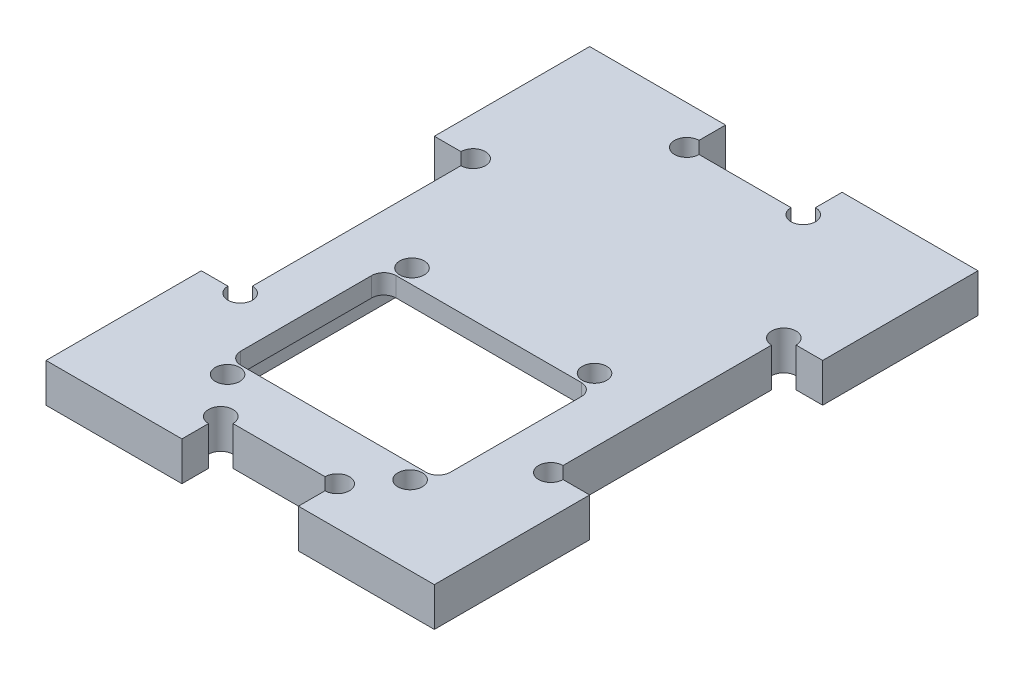
SolidWorks part; units mm, degrees
material "Acrylic (Medium-high impact)"
ref_plane "Front Plane" through (0, 0, 0) normal (0, 0, 1) x (1, 0, 0)
ref_plane "Top Plane" through (0, 0, 0) normal (0, 1, 0) x (1, 0, 0)
ref_plane "Right Plane" through (0, 0, 0) normal (1, 0, 0) x (0, 0, -1)
sketch "Sketch1" plane through (0, 0, 0) normal (0, 1, 0) x (1, 0, 0)
  line L1 (0, 0) -> (50, 0)
  line L2 (0, 0) -> (0, 70)
  line L3 (0, 70) -> (50, 70)
  line L4 (50, 0) -> (50, 70)
  line L5 (13.0748, 12) -> (36.9252, 12)
  line L6 (11.5, 13.5748) -> (11.5, 30.4252)
  line L7 (13.0748, 32) -> (36.9252, 32)
  line L8 (38.5, 13.5748) -> (38.5, 30.4252)
  arc A0 (36.9252, 12) -> (38.5, 13.5748) centre (36.9252, 13.5748) ccw
  arc A1 (38.5, 30.4252) -> (36.9252, 32) centre (36.9252, 30.4252) ccw
  arc A2 (13.0748, 32) -> (11.5, 30.4252) centre (13.0748, 30.4252) ccw
  arc A3 (13.0748, 12) -> (11.5, 13.5748) centre (13.0748, 13.5748) cw
  point P9 (25, 70)
  point P10 (25, 32)
  dimension "D7" = 1.5748
  dimension "D1" = 70
  dimension "D2" = 50
  dimension "D3" = 20
  dimension "D4" = 27
  dimension "D5" = 38
extrude "Boss-Extrude1" add sketch "Sketch1" along normal blind 5
sketch "Sketch2" plane through (0, 0, 0) normal (0, -1, 0) x (1, 0, 0)
  line L1 (12.0748, -37) -> (37.9252, -37)
  line L2 (10.5, -35.4252) -> (10.5, -8.5748)
  line L3 (12.0748, -7) -> (37.9252, -7)
  line L4 (39.5, -35.4252) -> (39.5, -8.5748)
  line L5 (10.5, -37) -> (39.5, -7) construction
  line L6 (10.5, -7) -> (39.5, -37) construction
  line L13 (11.5, -30.4252) -> (11.5, -13.5748) construction
  line L14 (11.5, -22) -> (38.5, -22) construction
  line L15 (38.5, -13.5748) -> (38.5, -30.4252) construction
  arc A0 (12.0748, -7) -> (10.5, -8.5748) centre (12.0748, -8.5748) ccw
  arc A1 (10.5, -35.4252) -> (12.0748, -37) centre (12.0748, -35.4252) ccw
  arc A2 (37.9252, -37) -> (39.5, -35.4252) centre (37.9252, -35.4252) ccw
  arc A3 (39.5, -8.5748) -> (37.9252, -7) centre (37.9252, -8.5748) ccw
  point P0 (25, -22)
  point P9 (25, -22)
  dimension "D1" = 1.5748
  dimension "D2" = 30
  dimension "D3" = 1
extrude "Cut-Extrude1" cut sketch "Sketch2" against normal blind 2.5
sketch "Sketch3" plane through (0, 5, 0) normal (0, 1, 0) x (1, 0, 0)
  line L0 (13.0748, 32) -> (36.9252, 12) construction
  line L1 (13.25, 10.125) -> (36.75, 10.125) construction
  line L2 (13.25, 10.125) -> (13.25, 33.875) construction
  line L3 (13.25, 33.875) -> (36.75, 33.875) construction
  line L4 (36.75, 10.125) -> (36.75, 33.875) construction
  line L5 (13.25, 10.125) -> (36.75, 33.875) construction
  line L6 (13.25, 33.875) -> (36.75, 10.125) construction
  line L7 (36.9252, 32) -> (13.0748, 32) construction
  circle A0 centre (13.25, 33.875) radius 1.5748
  circle A1 centre (36.75, 33.875) radius 1.5748
  circle A2 centre (36.75, 10.125) radius 1.5748
  circle A3 centre (13.25, 10.125) radius 1.5748
  point P0 (25, 22)
  point P5 (25, 22)
  dimension "D3" = 3.1496
  dimension "D1" = 23.75
  dimension "D2" = 23.5
extrude "Cut-Extrude5" cut sketch "Sketch3" against normal through all
sketch "Sketch4" plane through (0, 0, 0) normal (0, -1, 0) x (1, 0, 0)
  line L1 (34.1752, -61) -> (15.8248, -61)
  line L2 (35.75, -59.4252) -> (35.75, -43.0748)
  line L3 (34.1752, -41.5) -> (15.8248, -41.5)
  line L4 (14.25, -59.4252) -> (14.25, -43.0748)
  line L5 (35.75, -61) -> (14.25, -41.5) construction
  line L6 (35.75, -41.5) -> (14.25, -61) construction
  line L7 (50, -70) -> (0, -70) construction
  arc A0 (15.8248, -61) -> (14.25, -59.4252) centre (15.8248, -59.4252) cw
  arc A1 (34.1752, -61) -> (35.75, -59.4252) centre (34.1752, -59.4252) ccw
  arc A2 (35.75, -43.0748) -> (34.1752, -41.5) centre (34.1752, -43.0748) ccw
  arc A3 (14.25, -43.0748) -> (15.8248, -41.5) centre (15.8248, -43.0748) cw
  point P0 (25, -51.25)
  dimension "D3" = 1.5748
  dimension "D1" = 19.5
  dimension "D2" = 21.5
  dimension "D4" = 9
extrude "Cut-Extrude2" cut sketch "Sketch4" against normal blind 2.5
sketch "Sketch5" plane through (0, 5, 0) normal (0, 1, 0) x (1, 0, 0)
  line L0 (0, 70) -> (0, 0) construction
  line L1 (0, 20) -> (5, 20)
  line L2 (0, 20) -> (0, 50)
  line L3 (0, 50) -> (5, 50)
  line L4 (5, 20) -> (5, 50)
  line L5 (50, 70) -> (0, 70) construction
  line L6 (32.5, 70) -> (17.5, 70)
  line L7 (32.5, 70) -> (32.5, 65)
  line L8 (32.5, 65) -> (17.5, 65)
  line L9 (17.5, 70) -> (17.5, 65)
  line L10 (50, 0) -> (50, 70) construction
  line L11 (50, 50) -> (45, 50)
  line L12 (50, 50) -> (50, 20)
  line L13 (50, 20) -> (45, 20)
  line L14 (45, 50) -> (45, 20)
  line L15 (0, 0) -> (50, 0) construction
  line L16 (17.5, 0) -> (32.5, 0)
  line L17 (17.5, 0) -> (17.5, 5)
  line L18 (17.5, 5) -> (32.5, 5)
  line L19 (32.5, 0) -> (32.5, 5)
  point P25 (0, 35)
  point P26 (25, 0)
  dimension "D1" = 5
  dimension "D2" = 30
  dimension "D3" = 15
extrude "Cut-Extrude3" cut sketch "Sketch5" against normal through all both and the other way through all
sketch "Sketch6" plane through (0, 0, 0) normal (0, -1, 0) x (1, 0, 0)
  line L0 (17.5, -65) -> (32.5, -65) construction
  circle A0 centre (5, -50) radius 1.5748
  circle A1 centre (5, -20) radius 1.5748
  circle A2 centre (17.5, -5) radius 1.5748
  circle A3 centre (32.5, -5) radius 1.5748
  circle A4 centre (45, -20) radius 1.5748
  circle A5 centre (45, -50) radius 1.5748
  circle A6 centre (32.5, -65) radius 1.5748
  circle A7 centre (17.5, -65) radius 1.5748
  point P24 (14.0587, -65)
  point P26 (48.4796, -21.5034)
  point P27 (0, 0)
  dimension "D1" = 3.1496
extrude "Cut-Extrude4" cut sketch "Sketch6" against normal through all
equation "\"cortador\"= 8 / .1in"
equation "\"D1@Sketch6\"=\"cortador\""
equation "\"D3@Sketch4\"=\"cortador\"/2"
equation "\"D7@Sketch1\"=\"cortador\"/2"
equation "\"D3@Sketch3\"=\"cortador\""
equation "\"D1@Sketch2\"=\"cortador\"/2"
